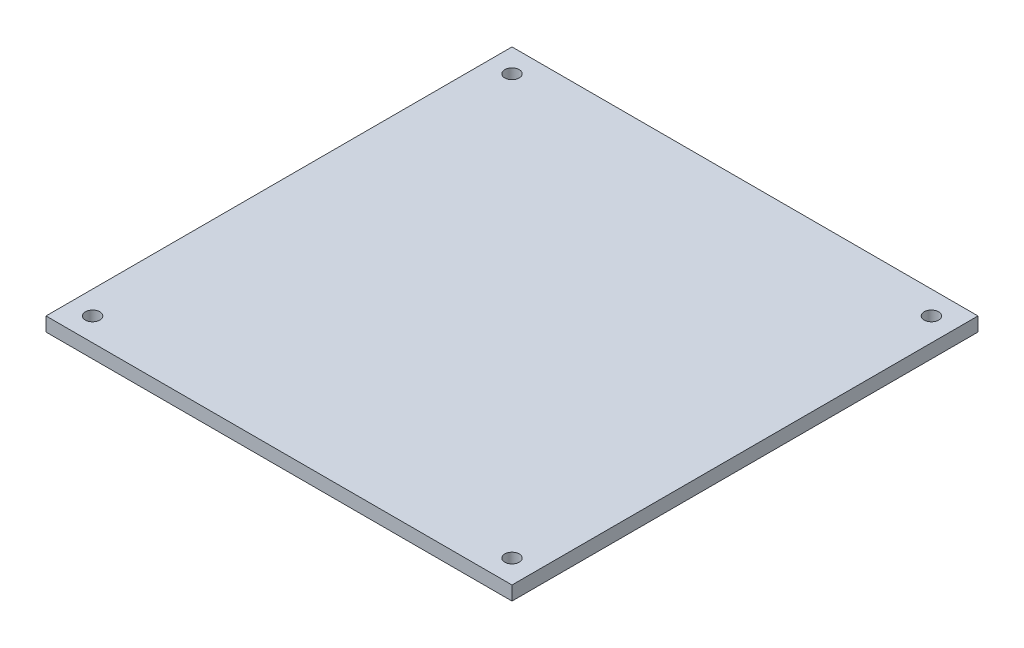
SolidWorks part; units mm, degrees
ref_plane "Front Plane" through (0, 0, 0) normal (0, 0, 1) x (1, 0, 0)
ref_plane "Top Plane" through (0, 0, 0) normal (0, 1, 0) x (1, 0, 0)
ref_plane "Right Plane" through (0, 0, 0) normal (1, 0, 0) x (0, 0, -1)
sketch "Sketch1" plane through (0, 0, 0) normal (0, 1, 0) x (1, 0, 0)
  line L1 (-50, -50) -> (50, -50)
  line L2 (-50, -50) -> (-50, 50)
  line L3 (-50, 50) -> (50, 50)
  line L4 (50, -50) -> (50, 50)
  line L5 (0, 50) -> (0, -50) construction
  line L6 (-50, 0) -> (50, 0) construction
  circle A0 centre (-45, -45) radius 1.55
  circle A1 centre (45, -45) radius 1.55
  circle A2 centre (45, 45) radius 1.55
  circle A3 centre (-45, 45) radius 1.55
  point P0 (0, 0)
  dimension "D1" = 3.1
  dimension "D2" = 100
  dimension "D3" = 100
  dimension "D4" = 5
  dimension "D5" = 5
extrude "Boss-Extrude1" add sketch "Sketch1" along normal blind 3
